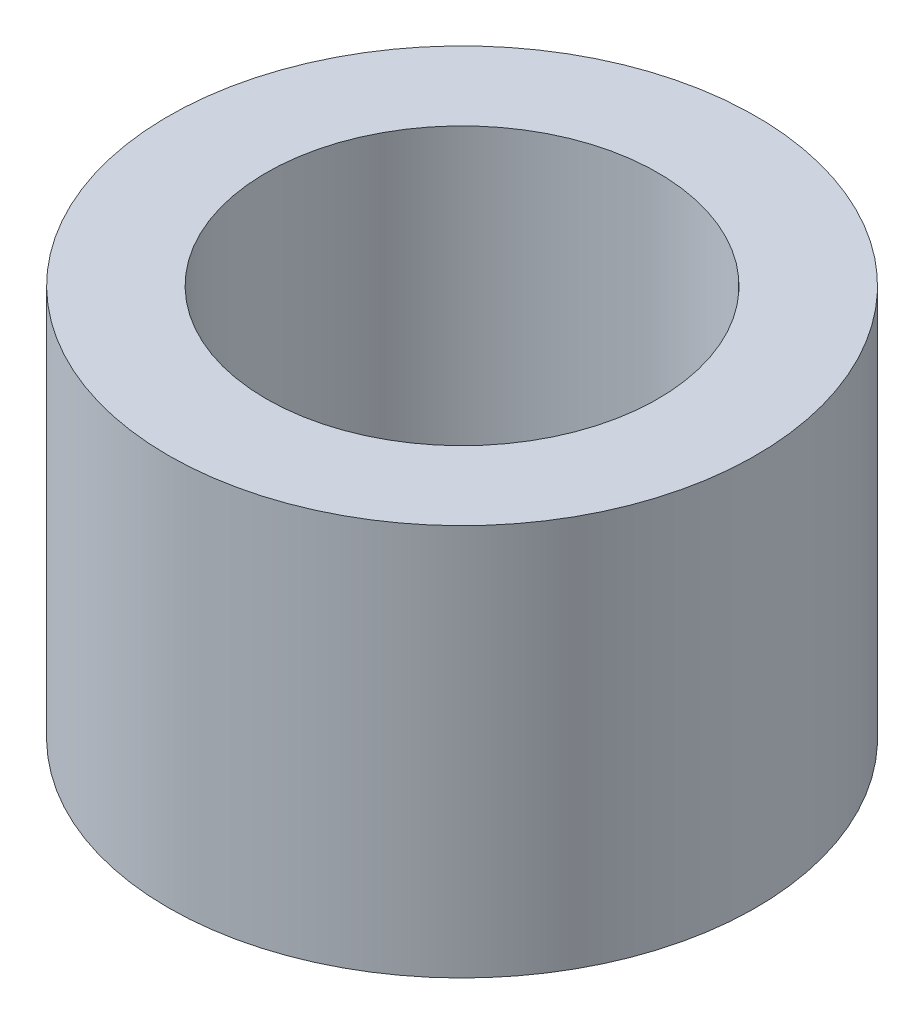
SolidWorks part; units mm, degrees
ref_plane "Front Plane" through (0, 0, 0) normal (0, 0, 1) x (1, 0, 0)
ref_plane "Top Plane" through (0, 0, 0) normal (0, 1, 0) x (1, 0, 0)
ref_plane "Right Plane" through (0, 0, 0) normal (1, 0, 0) x (0, 0, -1)
sketch "Sketch1" plane through (0, 0, 0) normal (0, 1, 0) x (1, 0, 0)
  circle A0 centre (0, 0) radius 1.5875
  circle A1 centre (0, 0) radius 2.3813
  dimension "D1" = 4.7625
  dimension "D2" = 3.175
extrude "Boss-Extrude1" add sketch "Sketch1" along normal blind 3.175
